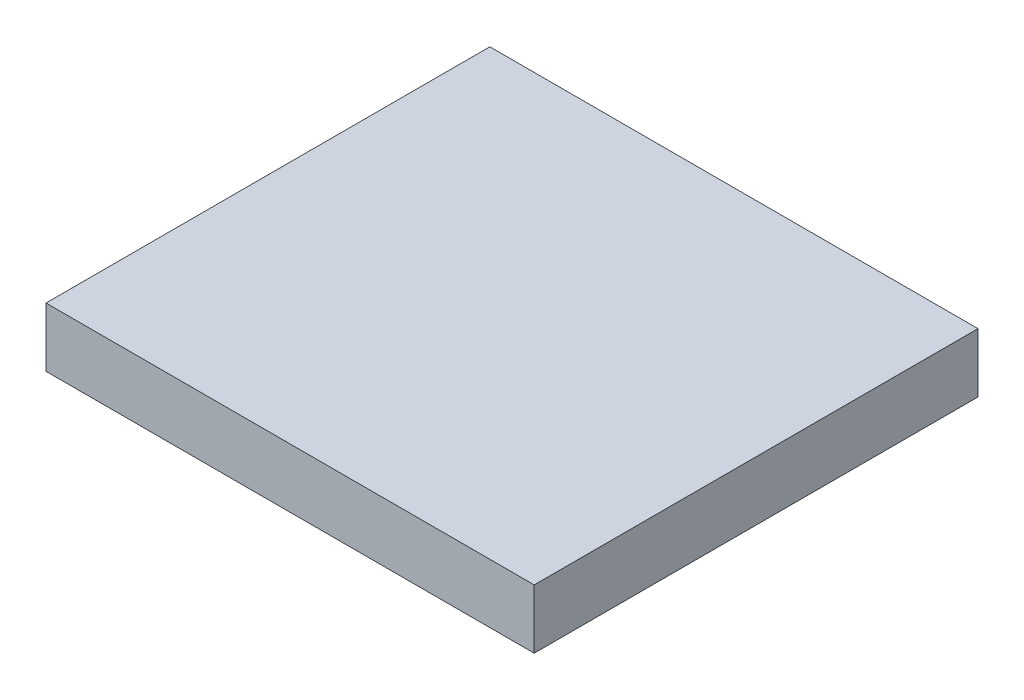
SolidWorks part; units mm, degrees
material "Copper"
ref_plane "Front Plane" through (0, 0, 0) normal (0, 0, 1) x (1, 0, 0)
ref_plane "Top Plane" through (0, 0, 0) normal (0, 1, 0) x (1, 0, 0)
ref_plane "Right Plane" through (0, 0, 0) normal (1, 0, 0) x (0, 0, -1)
sketch "Sketch1" plane through (0, 0, 0) normal (0, 1, 0) x (1, 0, 0)
  line L1 (-25.2593, 10.4775) -> (16.6507, 10.4775)
  line L2 (-25.2593, 10.4775) -> (-25.2593, -27.6225)
  line L3 (-25.2593, -27.6225) -> (16.6507, -27.6225)
  line L4 (16.6507, 10.4775) -> (16.6507, -27.6225)
  dimension "D1" = 41.91
  dimension "D2" = 38.1
extrude "Boss-Extrude1" add sketch "Sketch1" along normal blind 5.08
hole_wizard "Tap Drill for #4-48 Tap1" positions "Sketch4" profile "Sketch3" hole size "#4-48" standard "ANSI Inch"
sketch "Sketch4" plane through (-25.2593, 0, 0) normal (-1, 0, 0) x (0, 0, 1)
  line L1 (27.6225, 5.08) -> (27.6225, 0) construction
  point P0 (-0.3175, 2.4227)
  point P2 (22.5425, 2.4227)
  dimension "D1" = 22.86
  dimension "D2" = 5.08
sketch "Sketch3" plane through (-25.2593, 2.4227, -0.3175) normal (0, 1, 0) x (0, 0, 1)
  line L0 (0, 0) -> (0, 10.8735)
  line L1 (0, 10.8735) -> (1.1874, 10.16)
  line L2 (1.1874, 10.16) -> (1.1874, 0)
  line L5 (1.1874, 0) -> (0, 0)
  line L10 (0, 10.8735) -> (-1.1875, 10.16) construction
  line L11 (0, -6.35) -> (0, 107.95) construction
  dimension "Hole Dia." = 2.3749
  dimension "Hole Depth" = 10.16
  dimension "Drill Angle" = 118
